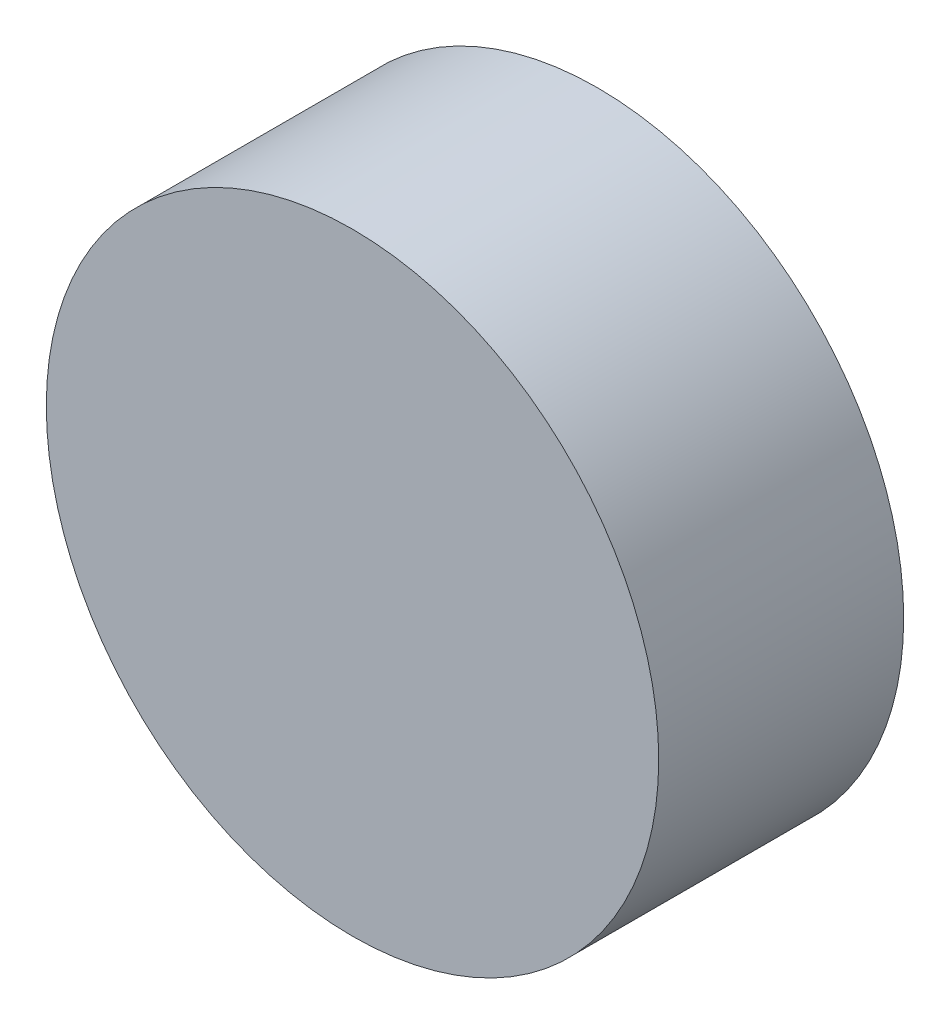
SolidWorks part; units mm, degrees
ref_plane "Front Plane" through (0, 0, 0) normal (0, 0, 1) x (1, 0, 0)
ref_plane "Top Plane" through (0, 0, 0) normal (0, 1, 0) x (1, 0, 0)
ref_plane "Right Plane" through (0, 0, 0) normal (1, 0, 0) x (0, 0, -1)
sketch "Sketch1" plane through (0, 0, 0) normal (0, 0, 1) x (1, 0, 0)
  circle A0 centre (0, 0) radius 2.5
  dimension "D1" = 5
extrude "Boss-Extrude1" add sketch "Sketch1" along normal mid plane 2
